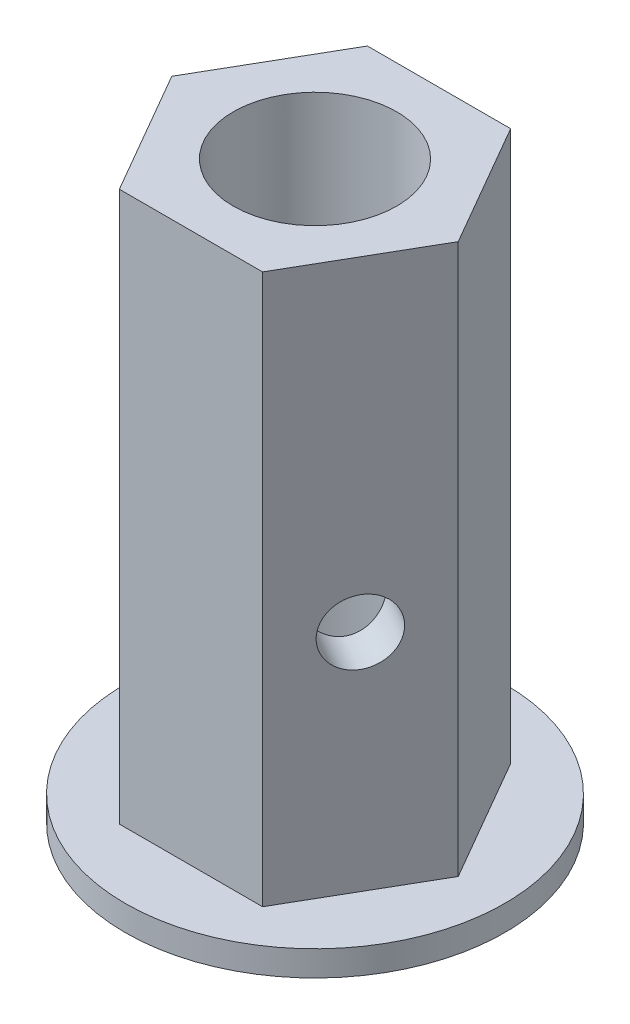
SolidWorks part; units mm, degrees
ref_plane "Front Plane" through (0, 0, 0) normal (0, 0, 1) x (1, 0, 0)
ref_plane "Top Plane" through (0, 0, 0) normal (0, 1, 0) x (1, 0, 0)
ref_plane "Right Plane" through (0, 0, 0) normal (1, 0, 0) x (0, 0, -1)
sketch "Sketch1" plane through (0, 0, 0) normal (0, 1, 0) x (1, 0, 0)
  line L1 (-3.5929, 6.223) -> (-7.1857, 0)
  line L2 (-7.1857, 0) -> (-3.5929, -6.223)
  line L3 (-3.5929, -6.223) -> (3.5929, -6.223)
  line L4 (3.5929, -6.223) -> (7.1857, 0)
  line L5 (7.1857, 0) -> (3.5929, 6.223)
  line L6 (3.5929, 6.223) -> (-3.5929, 6.223)
  circle A0 centre (0, 0) radius 6.223 construction
  dimension "D1" = 12.446
extrude "Boss-Extrude1" add sketch "Sketch1" along normal blind 27.5844
sketch "Sketch3" plane through (5.3893, 0, 3.1115) normal (0.866, 0, 0.5) x (0.5, 0, -0.866)
  line L0 (-3.5929, 0) -> (3.5929, 0) construction
  circle A0 centre (0, 11.2776) radius 1.6256
  dimension "D1" = 3.2512
  dimension "D2" = 11.2776
extrude "Cut-Extrude2" cut sketch "Sketch3" against normal through all contours A0
sketch "Sketch4" plane through (0, 0, 0) normal (0, -1, 0) x (1, 0, 0)
  circle A0 centre (0, 0) radius 9.525
  dimension "D1" = 19.05
extrude "Boss-Extrude3" add sketch "Sketch4" along normal blind 1.27
sketch "Sketch2" plane through (0, 27.5844, 0) normal (0, 1, 0) x (1, 0, 0)
  circle A0 centre (0, 0) radius 4.1021
  dimension "D1" = 8.2042
extrude "Cut-Extrude1" cut sketch "Sketch2" against normal through all contours A0
